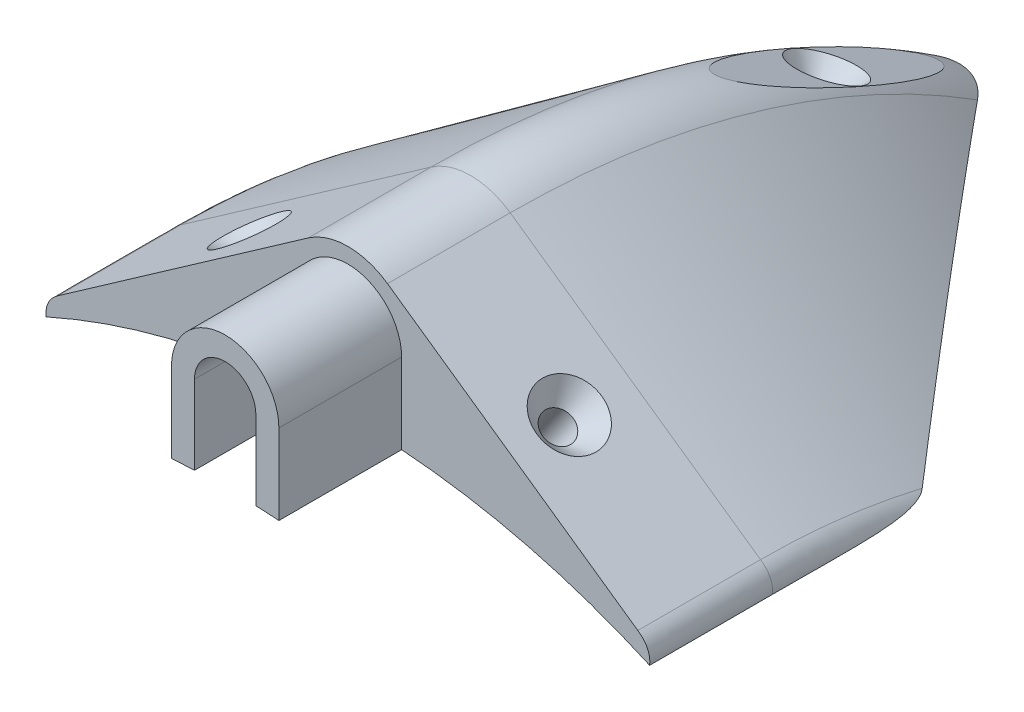
SolidWorks part; units mm, degrees
material "6061-T6 (SS)"
ref_plane "Front Plane" through (0, 0, 0) normal (0, 0, 1) x (1, 0, 0)
ref_plane "Top Plane" through (0, 0, 0) normal (0, 1, 0) x (1, 0, 0)
ref_plane "Right Plane" through (0, 0, 0) normal (1, 0, 0) x (0, 0, -1)
sketch "Sketch1" plane through (0, 0, 0) normal (0, 0, 1) x (1, 0, 0)
  line L0 (0, 0) -> (0, 152.4) construction
  line L1 (-59.9912, 144.0357) -> (-8.1938, 180.2969)
  line L7 (0, 0) -> (74.48, 0) construction
  line L20 (59.9912, 144.0357) -> (8.1938, 180.2969)
  arc A1 (8.1938, 180.2969) -> (-8.1938, 180.2969) centre (0, 168.5925) ccw
  arc A7 (62.4412, 139.0211) -> (-62.4412, 139.0211) centre (0, 0) ccw
  spline S2 degree 2 poles (-59.9912, 144.0357) (-62.7825, 142.084) (-62.4412, 139.0211) knots 0 0 0 1 1 1
  spline S3 degree 2 poles (59.9912, 144.0357) (62.7825, 142.084) (62.4412, 139.0211) knots 0 0 0 1 1 1
  dimension "D2" = 63.2286
  dimension "D3" = 28.575
  dimension "D12" = 5.8922
  dimension "D5" = 152.4
  dimension "D1" = 168.5925
  dimension "D4" = 51.7974
  dimension "D14" = 1.791
  dimension "D15" = 3.2237
revolve "Revolve1" add sketch "Sketch1" angle 57 about L7
sketch "Sketch3" plane through (0, 0, 0) normal (0, 0, 1) x (1, 0, 0)
  line L0 (0, 0) -> (0, 152.4) construction
  line L2 (-59.9912, 144.0357) -> (-8.1938, 180.2969)
  line L4 (19.2885, 0) -> (93.7685, 0) construction
  line L5 (59.9912, 144.0357) -> (8.1938, 180.2969)
  arc A2 (8.1938, 180.2969) -> (-8.1938, 180.2969) centre (0, 168.5925) ccw
  arc A3 (62.4412, 139.0211) -> (-62.4412, 139.0211) centre (0, 0) ccw
  spline S0 degree 2 poles (-59.9912, 144.0357) (-62.7825, 142.084) (-62.4412, 139.0211) knots 0 0 0 1 1 1
  spline S1 degree 2 poles (59.9912, 144.0357) (62.7825, 142.084) (62.4412, 139.0211) knots 0 0 0 1 1 1
  dimension "D2" = 28.575
  dimension "D3" = 5.8922
  dimension "D8" = 152.4
  dimension "D1" = 168.5925
  dimension "D4" = 1.791
  dimension "D5" = 3.2237
  dimension "D6" = 63.2286
  dimension "D7" = 51.7974
extrude "Boss-Extrude1" add sketch "Sketch3" along normal blind 25.4
ref_plane "Plane1" through (0, 0, 12.7) normal (0, 0, 1) x (1, 0, 0)
sketch "Sketch7" plane through (0, 0, 12.7) normal (0, 0, 1) x (1, 0, 0)
  line L0 (-30.5085, 164.6753) -> (-18.8551, 148.029) construction
  line L1 (-8.1938, 180.2969) -> (-59.9912, 144.0357) construction
  line L2 (-18.8551, 148.029) -> (-21.4561, 146.2082)
  line L3 (-21.4561, 146.2082) -> (-37.8066, 169.5641) construction
  line L4 (-30.7642, 159.5044) -> (-19.1086, 167.6641) construction
  line L5 (-21.4561, 146.2082) -> (-33.1095, 162.8545)
  line L6 (-18.8551, 148.029) -> (-28.1633, 161.3253)
  line L7 (-33.1095, 162.8545) -> (-27.585, 166.722)
  line L8 (-27.585, 166.722) -> (-28.1633, 161.3253)
  line L9 (0, 0) -> (0, 246.8513) construction
  circle A0 centre (0, 0) radius 152.4 construction
  circle A1 centre (0, 0) radius 149.225 construction
  dimension "D1" = 16.2306
  dimension "D2" = 3.175
  dimension "D3" = 4.0894
  dimension "D4" = 6.7437
revolve "Cut-Revolve2" cut sketch "Sketch7" angle 360 about L3
mirror "Mirror2" about plane through (0, 0, 0) normal (1, 0, 0) of "Cut-Revolve2"
sketch "Sketch8" plane through (0, 0, 25.4) normal (0, 0, 1) x (1, 0, 0)
  circle A0 centre (0, 0) radius 152.4
extrude "Cut-Extrude3" cut sketch "Sketch8" against normal blind 257.048
sketch "Sketch10" plane through (0, 0, 0) normal (1, 0, 0) x (0, 0, -1)
  line L0 (0, 0) -> (74.384, 167.0692) construction
  line L1 (0, 0) -> (0, 180.2969) construction
  line L2 (0, 0) -> (50.4086, 175.7955) construction
  line L3 (50.4086, 175.7955) -> (74.384, 167.0692) construction
  arc A1 (101.0907, 152.4) -> (0, 182.88) centre (0, 0) ccw construction
  dimension "D1" = 24
  dimension "D2" = 16
  dimension "D3" = 25.5141
ref_plane "Plane2" through (0, 167.0692, -74.384) normal (0, 0.9135, -0.4067) x (1, 0, 0)
sketch "Sketch13" plane through (0, 167.0692, -74.384) normal (0, 0.9135, -0.4067) x (1, 0, 0)
  line L0 (8.1938, 26.4309) -> (8.1938, -73.3334) construction
  line L1 (8.1938, 63.5) -> (-8.1938, 63.5)
  line L2 (8.1938, 63.5) -> (8.1938, -63.5)
  line L3 (8.1938, -63.5) -> (-8.1938, -63.5)
  line L4 (-8.1938, 63.5) -> (-8.1938, -63.5)
  line L5 (-8.1938, 26.4309) -> (-8.1938, -73.3334) construction
  dimension "D1" = 127
  dimension "D2" = 63.5
extrude "Cut-Extrude5" cut sketch "Sketch13" against normal blind 1.778
sketch "Sketch14" plane through (0, 0, 0) normal (1, 0, 0) x (0, 0, -1)
  line L0 (73.6608, 165.4449) -> (67.5001, 168.1878)
  line L1 (96.9008, 155.0978) -> (50.4208, 175.792) construction
  line L2 (73.6608, 165.4449) -> (63.3297, 142.2409)
  line L3 (0, 0) -> (74.384, 167.0692) construction
  line L4 (63.3297, 142.2409) -> (60.4292, 143.5322)
  line L5 (60.4292, 143.5322) -> (69.097, 163.0004)
  line L6 (67.5001, 168.1878) -> (69.097, 163.0004)
  dimension "D1" = 6.7437
  dimension "D2" = 25.4
  dimension "D3" = 3.175
  dimension "D4" = 21.3106
revolve "Cut-Revolve4" cut sketch "Sketch14" angle 360 about L2
sketch "Sketch15" plane through (0, 0, 25.4) normal (0, 0, 1) x (1, 0, 0)
  line L0 (0, 175.7955) -> (0, 167.0692) construction
  line L4 (0, 90.1485) -> (0, -57.1327) construction
  line L5 (-38.8192, 154.9817) -> (-34.2781, 148.495) construction
  line L7 (-40.64, 157.5827) -> (-38.8192, 154.9817) construction
  line L8 (-8.1938, 180.2969) -> (-59.9912, 144.0357) construction
  line L10 (-18.0112, 169.5485) -> (-5.9256, 152.2848) construction
  line L11 (-11.1125, 168.5925) -> (-11.1125, 151.9943)
  line L14 (11.1125, 168.5925) -> (11.1125, 151.9943)
  line L18 (-6.35, 168.5925) -> (-6.35, 152.2677)
  line L19 (6.35, 168.5925) -> (6.35, 152.2677)
  arc A1 (11.1125, 168.5925) -> (-11.1125, 168.5925) centre (0, 168.5925) ccw
  arc A2 (8.1938, 180.2969) -> (-8.1938, 180.2969) centre (0, 168.5925) ccw construction
  arc A3 (11.1125, 151.9943) -> (6.35, 152.2677) centre (0, 0) ccw
  arc A5 (6.35, 168.5925) -> (-6.35, 168.5925) centre (0, 168.5925) ccw
  arc A6 (-6.35, 152.2677) -> (-11.1125, 151.9943) centre (0, 0) ccw
  point P2 (0, 0)
  dimension "D1" = 152.4
  dimension "D2" = 11.1125
  dimension "D5" = 6.35
  dimension "D3" = 0
  dimension "D4" = 3.175
  dimension "D6" = 25.4
  dimension "D7" = 28.5087
  dimension "D8" = 18.0112
extrude "Boss-Extrude3" add sketch "Sketch15" along normal blind 25.4
